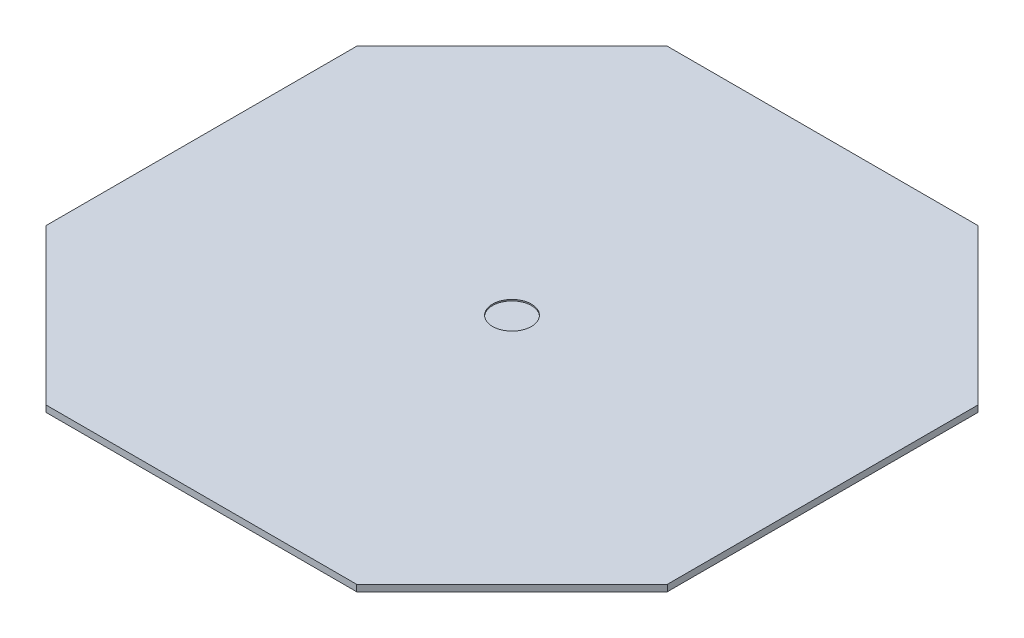
SolidWorks part; units mm, degrees
ref_plane "Front Plane" through (0, 0, 0) normal (0, 0, 1) x (1, 0, 0)
ref_plane "Top Plane" through (0, 0, 0) normal (0, 1, 0) x (1, 0, 0)
ref_plane "Right Plane" through (0, 0, 0) normal (1, 0, 0) x (0, 0, -1)
sketch "Sketch1" plane through (0, 0, 0) normal (0, 1, 0) x (1, 0, 0)
  line L0 (-304.8, 609.6) -> (304.8, 609.6)
  line L1 (304.8, 609.6) -> (609.6, 304.8)
  line L2 (609.6, 304.8) -> (609.6, -304.8)
  line L3 (609.6, -304.8) -> (304.8, -609.6)
  line L4 (304.8, -609.6) -> (-304.8, -609.6)
  line L5 (-304.8, -609.6) -> (-609.6, -304.8)
  line L6 (-609.6, -304.8) -> (-609.6, 304.8)
  line L8 (609.6, 304.8) -> (609.6, -304.8)
  line L9 (304.8, -609.6) -> (-304.8, -609.6)
  line L10 (-609.6, 304.8) -> (-609.6, -304.8)
  line L11 (457.2, 457.2) -> (-457.2, -457.2) construction
  line L12 (457.2, -457.2) -> (-457.2, 457.2) construction
  line L13 (-609.6, 304.8) -> (-304.8, 609.6)
  point P0 (0, 0)
  dimension "D1" = 609.6
  dimension "D5" = 609.6
  dimension "D7" = 609.6
extrude "Boss-Extrude1" add sketch "Sketch1" along normal blind 12.7 contours L13 L6 L5 L4 L3 L2 L1 L0
sketch "Sketch2" plane through (0, 12.7, 0) normal (0, 1, 0) x (1, 0, 0)
  circle A0 centre (0, 0) radius 38.1
  dimension "D1" = 76.2
sketch "Sketch3" plane through (0, 12.7, 0) normal (0, 1, 0) x (1, 0, 0)
extrude "Cut-Extrude1" cut sketch "Sketch2" against normal blind 2.54
